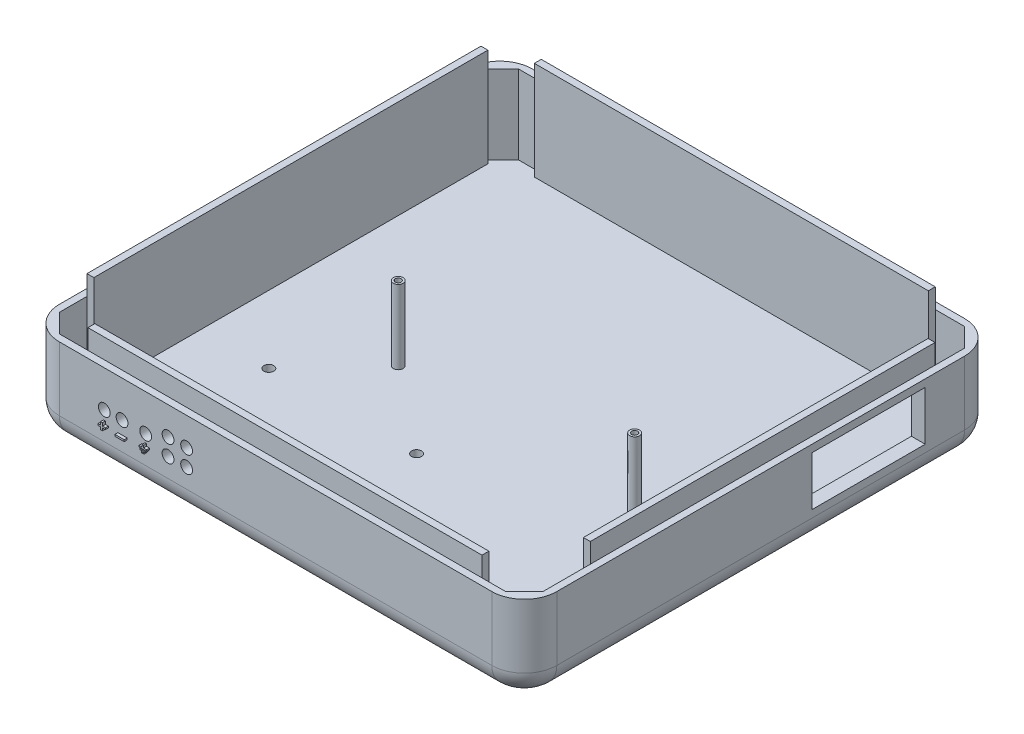
SolidWorks part; units mm, degrees
ref_plane "Front Plane" through (0, 0, 0) normal (0, 0, 1) x (1, 0, 0)
ref_plane "Top Plane" through (0, 0, 0) normal (0, 1, 0) x (1, 0, 0)
ref_plane "Right Plane" through (0, 0, 0) normal (1, 0, 0) x (0, 0, -1)
sketch "Sketch1" plane through (0, 0, 0) normal (0, 1, 0) x (1, 0, 0)
  line L1 (-63.2516, -37.0743) -> (44.6984, -37.0743)
  line L2 (-63.2516, -37.0743) -> (-63.2516, 64.5257)
  line L3 (-63.2516, 64.5257) -> (44.6984, 64.5257)
  line L4 (44.6984, -37.0743) -> (44.6984, 64.5257)
  dimension "D1" = 101.6
extrude "Boss-Extrude1" add sketch "Sketch1" along normal blind 2.54
sketch "Sketch4" plane through (0, 2.54, 0) normal (0, 1, 0) x (1, 0, 0)
  circle A0 centre (-36.3276, 11.4397) radius 1.27
  circle A1 centre (28.1884, 7.8837) radius 1.27
  circle A3 centre (-36.3276, 11.4397) radius 0.762
  circle A4 centre (28.1884, 7.8837) radius 0.762
sketch "Sketch17" plane through (0, 0, -64.5257) normal (0, 0, -1) x (-1, 0, 0)
  line L1 (-44.6984, 2.54) -> (63.2516, 2.54)
  line L2 (-44.6984, 2.54) -> (-44.6984, 0)
  line L3 (-44.6984, 0) -> (63.2516, 0)
  line L4 (63.2516, 2.54) -> (63.2516, 0)
extrude "Boss-Extrude11" add sketch "Sketch17" along normal blind 10.16
sketch "Sketch19" plane through (0, 2.54, 0) normal (0, 1, 0) x (1, 0, 0)
  line L2 (38.8354, 64.5257) -> (-63.2516, 64.5257) construction
  line L3 (-63.2516, 74.6857) -> (-63.2516, -37.0743) construction
sketch "Sketch20" plane through (44.6984, 0, 0) normal (1, 0, 0) x (0, 0, -1)
  line L1 (-37.0743, 2.54) -> (74.6857, 2.54)
  line L2 (-37.0743, 2.54) -> (-37.0743, 0)
  line L3 (-37.0743, 0) -> (74.6857, 0)
  line L4 (74.6857, 2.54) -> (74.6857, 0)
extrude "Boss-Extrude12" add sketch "Sketch20" along normal blind 10.16
sketch "Sketch21" plane through (0, 0, 37.0743) normal (0, 0, 1) x (1, 0, 0)
  line L1 (-63.2516, 2.54) -> (54.8584, 2.54)
  line L2 (-63.2516, 2.54) -> (-63.2516, 0)
  line L3 (-63.2516, 0) -> (54.8584, 0)
  line L4 (54.8584, 2.54) -> (54.8584, 0)
extrude "Boss-Extrude13" add sketch "Sketch21" along normal blind 10.16
sketch "Sketch22" plane through (-63.2516, 0, 0) normal (-1, 0, 0) x (0, 0, 1)
  line L1 (-74.6857, 2.54) -> (47.2343, 2.54)
  line L2 (-74.6857, 2.54) -> (-74.6857, 0)
  line L3 (-74.6857, 0) -> (47.2343, 0)
  line L4 (47.2343, 2.54) -> (47.2343, 0)
extrude "Boss-Extrude14" add sketch "Sketch22" along normal blind 10.16
sketch "Sketch26" plane through (0, 2.54, 0) normal (0, 1, 0) x (1, 0, 0)
  line L0 (42.7116, -45.4563) -> (-66.8076, -45.4563)
  line L1 (-71.6336, -37.537) -> (-71.6336, 66.3037)
  line L3 (-73.4116, 74.6857) -> (54.8584, 74.6857)
  line L4 (-73.4116, 74.6857) -> (-73.4116, -47.2343)
  line L5 (-73.4116, -47.2343) -> (54.8584, -47.2343)
  line L6 (-62.2781, 72.9077) -> (48.2544, 72.9077)
  line L7 (54.8584, 74.6857) -> (54.8584, -47.2343)
  line L15 (53.0804, 68.0817) -> (53.0804, -38.8523)
  line L16 (53.0804, -38.8523) -> (53.0804, -40.6303)
  line L19 (42.7116, -45.4563) -> (48.2544, -45.4563)
  line L20 (48.2544, -45.4563) -> (53.0804, -40.6303)
  line L23 (-71.6336, -37.537) -> (-71.6336, -40.6303)
  line L24 (-71.6336, -40.6303) -> (-66.8076, -45.4563)
  line L25 (-71.6336, 66.3037) -> (-71.6336, 68.0817)
  line L28 (-62.2781, 72.9077) -> (-66.8076, 72.9077)
  line L29 (-66.8076, 72.9077) -> (-71.6336, 68.0817)
  line L30 (48.2544, 72.9077) -> (53.0804, 68.0817)
extrude "Boss-Extrude18" add sketch "Sketch26" along normal blind 20.32
fillet "Fillet9" radius 8.382 1 edges at (-73.4116, 11.43, 47.2343)
fillet "Fillet10" radius 8.382 1 edges at (54.8584, 11.43, 47.2343)
fillet "Fillet11" radius 8.382 1 edges at (-73.4116, 11.43, -74.6857)
sketch "Sketch28" plane through (0, 2.54, 0) normal (0, 1, 0) x (1, 0, 0)
  line L0 (-66.8076, -45.4563) -> (48.2544, -45.4563) construction
  line L1 (42.1565, -45.4563) -> (-59.4435, -45.4563)
  line L2 (42.1565, -45.4563) -> (42.1565, -43.6783)
  line L3 (42.1565, -43.6783) -> (-59.4435, -43.6783)
  line L4 (-59.4435, -45.4563) -> (-59.4435, -43.6783)
extrude "Boss-Extrude21" add sketch "Sketch28" along normal blind 25.4
sketch "Sketch29" plane through (0, 2.54, 0) normal (0, 1, 0) x (1, 0, 0)
  line L0 (53.0804, -40.6303) -> (53.0804, 68.0817) construction
  line L1 (53.0804, -28.446) -> (51.3024, -28.446)
  line L2 (53.0804, -28.446) -> (53.0804, 60.454)
  line L3 (53.0804, 60.454) -> (51.3024, 60.454)
  line L4 (51.3024, -28.446) -> (51.3024, 60.454)
extrude "Boss-Extrude22" add sketch "Sketch29" along normal blind 25.4
fillet "Fillet21" radius 8.382 1 edges at (54.8584, 11.43, -74.6857)
sketch "Sketch30" plane through (0, 2.54, 0) normal (0, 1, 0) x (1, 0, 0)
  line L0 (48.2544, 72.9077) -> (-66.8076, 72.9077) construction
  line L1 (-60.9177, 72.9077) -> (40.6823, 72.9077)
  line L2 (-60.9177, 72.9077) -> (-60.9177, 71.1297)
  line L3 (-60.9177, 71.1297) -> (40.6823, 71.1297)
  line L4 (40.6823, 72.9077) -> (40.6823, 71.1297)
extrude "Boss-Extrude23" add sketch "Sketch30" along normal blind 25.4
sketch "Sketch31" plane through (0, 2.54, 0) normal (0, 1, 0) x (1, 0, 0)
  line L0 (-71.6336, 68.0817) -> (-71.6336, -40.6303) construction
  line L1 (-71.6336, 68.0815) -> (-69.8556, 68.0815)
  line L2 (-71.6336, 68.0815) -> (-71.6336, -33.5185)
  line L3 (-71.6336, -33.5185) -> (-69.8556, -33.5185)
  line L4 (-69.8556, 68.0815) -> (-69.8556, -33.5185)
extrude "Boss-Extrude24" add sketch "Sketch31" along normal blind 25.4
sketch "Sketch32" plane through (0, 0, 47.2343) normal (0, 0, 1) x (1, 0, 0)
  circle A0 centre (-53.4461, 13.4684) radius 1.524
  circle A1 centre (-48.8741, 13.4684) radius 1.524
  circle A2 centre (-42.7781, 13.4684) radius 1.524
extrude "Cut-Extrude1" cut sketch "Sketch32" against normal blind 3.556
fillet "Fillet22" radius 6.35 8 edges at (-70.9565, 0, -72.2307) (-9.2766, 0, -74.6857) (52.4034, 0, -72.2307) (54.8584, 0, -13.7257) (52.4034, 0, 44.7793) (-9.2766, 0, 47.2343) (-70.9565, 0, 44.7793) (-73.4116, 0, -13.7257)
sketch "Sketch34" plane through (0, 0, 47.2343) normal (0, 0, 1) x (1, 0, 0)
  line L1 (-49.9348, 10.1314) -> (-47.5584, 10.1314)
  line L2 (-49.9348, 10.1314) -> (-49.9348, 9.6805)
  line L3 (-49.9348, 9.6805) -> (-47.5584, 9.6805)
  line L4 (-47.5584, 10.1314) -> (-47.5584, 9.6805)
extrude "Boss-Extrude26" add sketch "Sketch34" along normal blind 0.762
sketch "Sketch35" plane through (0, 0, 47.2343) normal (0, 0, 1) x (1, 0, 0)
  line L0 (-53.675, 11.1079) -> (-53.1829, 11.1079)
  line L1 (-53.1829, 11.1079) -> (-53.1829, 10.3454)
  line L2 (-53.1829, 10.3454) -> (-52.4152, 10.3454)
  line L3 (-52.4152, 10.3454) -> (-52.4152, 9.9413)
  line L4 (-52.4152, 9.9413) -> (-53.1829, 9.9413)
  line L5 (-53.1829, 9.9413) -> (-53.1829, 9.2855)
  line L6 (-53.1829, 9.2855) -> (-53.675, 9.2855)
  line L7 (-53.675, 9.2855) -> (-53.675, 9.9413)
  line L8 (-53.675, 9.9413) -> (-54.3329, 9.9413)
  line L9 (-54.3329, 9.9413) -> (-54.3329, 10.3454)
  line L10 (-54.3329, 10.3454) -> (-53.675, 10.3454)
  line L11 (-53.675, 10.3454) -> (-53.675, 11.1079)
extrude "Boss-Extrude27" add sketch "Sketch35" along normal blind 0.762
sketch "Sketch36" plane through (0, 0, 47.2343) normal (0, 0, 1) x (1, 0, 0)
  line L0 (-42.9384, 11.3911) -> (-42.5709, 11.3911)
  line L1 (-42.5709, 11.3911) -> (-42.5709, 10.7748)
  line L2 (-42.5709, 10.7748) -> (-41.7736, 10.7748)
  line L3 (-41.7736, 10.7748) -> (-41.7736, 10.4215)
  line L4 (-41.7736, 10.4215) -> (-43.749, 10.4215)
  line L5 (-43.749, 10.4215) -> (-43.749, 10.7748)
  line L6 (-43.749, 10.7748) -> (-42.9384, 10.7748)
  line L7 (-42.9384, 10.7748) -> (-42.9384, 11.3911)
  line L8 (-42.9384, 11.3911) -> (-42.9922, 11.3173)
extrude "Boss-Extrude28" add sketch "Sketch36" along normal blind 0.762 contours L7 L6 L5 L4 L3 L2 L1 L0
sketch "Sketch37" plane through (0, 0, 47.2343) normal (0, 0, 1) x (1, 0, 0)
  line L1 (-43.4804, 10.2464) -> (-42.0787, 10.2464)
  line L2 (-43.4804, 10.2464) -> (-43.4804, 9.9504)
  line L3 (-43.4804, 9.9504) -> (-42.0787, 9.9504)
  line L4 (-42.0787, 10.2464) -> (-42.0787, 9.9504)
extrude "Boss-Extrude29" add sketch "Sketch37" along normal blind 0.762
sketch "Sketch38" plane through (0, 0, 47.2343) normal (0, 0, 1) x (1, 0, 0)
  line L1 (-43.1463, 9.7082) -> (-42.4249, 9.7082)
  line L2 (-43.1463, 9.7082) -> (-43.1463, 9.4583)
  line L3 (-43.1463, 9.4583) -> (-42.4249, 9.4583)
  line L4 (-42.4249, 9.7082) -> (-42.4249, 9.4583)
extrude "Boss-Extrude30" add sketch "Sketch38" along normal blind 0.762
extrude "Boss-Extrude31" add sketch "Sketch4" along normal blind 19.05
sketch "Sketch40" plane through (0, 0, 47.2343) normal (0, 0, 1) x (1, 0, 0)
  circle A0 centre (-37.0123, 15.6148) radius 1.524
  circle A1 centre (-32.2235, 15.6148) radius 1.524
  circle A2 centre (-37.0123, 11.2913) radius 1.524
  circle A3 centre (-32.2235, 11.2913) radius 1.524
extrude "Cut-Extrude2" cut sketch "Sketch40" against normal blind 3.556
sketch "Sketch42" plane through (54.8584, 0, 0) normal (1, 0, 0) x (0, 0, -1)
  line L3 (56.1437, 20.955) -> (26.9337, 20.955)
  line L4 (56.1437, 20.955) -> (56.1437, 8.255)
  line L5 (56.1437, 8.255) -> (26.9337, 8.255)
  line L6 (26.9337, 20.955) -> (26.9337, 8.255)
extrude "Cut-Extrude3" cut sketch "Sketch42" against normal blind 3.556
sketch "Sketch43" plane through (0, 2.54, 0) normal (0, 1, 0) x (1, 0, 0)
  circle A4 centre (-14.3239, -5.8308) radius 1.27
  circle A5 centre (-52.4239, -5.8308) radius 1.27
  circle A6 centre (-52.4239, -38.8508) radius 1.27
  circle A7 centre (-14.3239, -38.8508) radius 1.27
extrude "Cut-Extrude4" cut sketch "Sketch43" against normal blind 2.54
